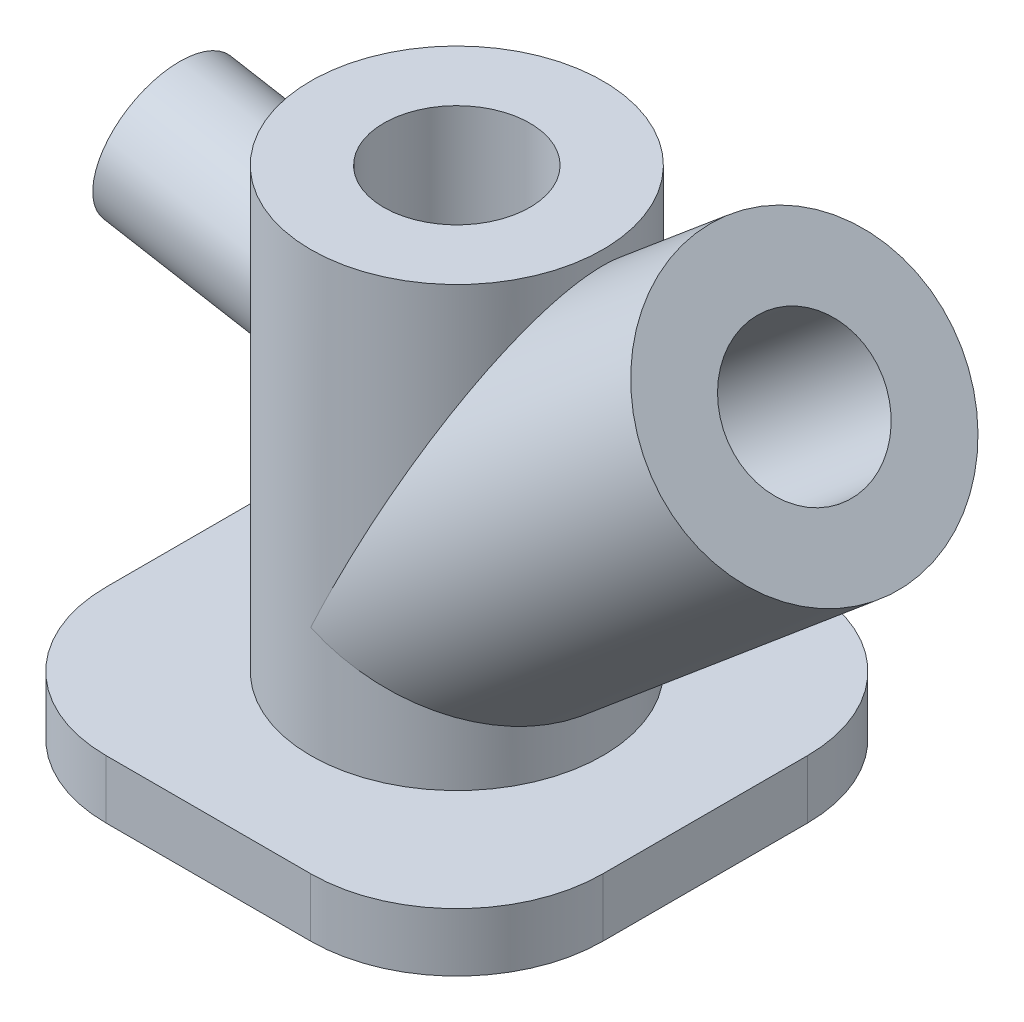
SolidWorks part; units mm, degrees
ref_plane "Front Plane" through (0, 0, 0) normal (0, 0, 1) x (1, 0, 0)
ref_plane "Top Plane" through (0, 0, 0) normal (0, 1, 0) x (1, 0, 0)
ref_plane "Right Plane" through (0, 0, 0) normal (1, 0, 0) x (0, 0, -1)
sketch "Sketch2" plane through (0, 0, 0) normal (0, 1, 0) x (1, 0, 0)
  line L1 (35, -85) -> (-35, -85)
  line L2 (85, -35) -> (85, 35)
  line L3 (35, 85) -> (-35, 85)
  line L4 (-85, -35) -> (-85, 35)
  line L5 (85, -85) -> (-85, 85) construction
  line L6 (85, 85) -> (-85, -85) construction
  arc A0 (-85, 35) -> (-35, 85) centre (-35, 35) cw
  arc A1 (-35, -85) -> (-85, -35) centre (-35, -35) cw
  arc A2 (85, -35) -> (35, -85) centre (35, -35) cw
  arc A3 (35, 85) -> (85, 35) centre (35, 35) cw
  point P0 (0, 0)
  dimension "D3" = 50
  dimension "D4" = 50
  dimension "D5" = 50
  dimension "D6" = 50
  dimension "D1" = 170
  dimension "D2" = 170
extrude "Boss-Extrude1" add sketch "Sketch2" along normal blind 20
sketch "Sketch3" plane through (0, 20, 0) normal (0, 1, 0) x (1, 0, 0)
  circle A0 centre (0, 0) radius 50
extrude "Boss-Extrude2" add sketch "Sketch3" along normal blind 150
sketch "Sketch4" plane through (0, 170, 0) normal (0, 1, 0) x (1, 0, 0)
  circle A0 centre (0, 0) radius 25
extrude "Cut-Extrude1" cut sketch "Sketch4" against normal blind 170
sketch "Sketch5" plane through (0, 0, 0) normal (0, 0, 1) x (1, 0, 0)
  line L0 (50, 100) -> (118.944, 157.8509) construction
  line L1 (98.4197, 182.3108) -> (154.7708, 115.1542) construction
  line L2 (50, 20) -> (50, 170) construction
  line L3 (85, 20) -> (35, 20) construction
  point P6 (0, 0)
  point P7 (0, 0)
  point P10 (0, 0)
  dimension "D1" = 80
  dimension "D2" = 130
  dimension "D3" = 90
ref_plane "Plane1" through (147.5256, 123.7887, 0) normal (0.766, 0.6428, 0) x (0, 0, -1)
sketch "Sketch6" plane through (147.5256, 123.7887, 0) normal (0.766, 0.6428, 0) x (0, 0, -1)
  circle A0 centre (0, 44.4651) radius 50
extrude "Boss-Extrude4" add sketch "Sketch6" against normal up to next
sketch "Sketch7" plane through (147.5256, 123.7887, 0) normal (0.766, 0.6428, 0) x (0, 0, -1)
  circle A0 centre (0, 44.4651) radius 25
extrude "Cut-Extrude2" cut sketch "Sketch7" against normal up to next and the other way through all
sketch "Sketch8" plane through (0, 0, 0) normal (0, 0, 1) x (1, 0, 0)
  line L0 (-99.2404, 128.6824) -> (-50, 120) construction
  line L1 (-102.3273, 111.1759) -> (-95.4373, 150.2509) construction
  line L2 (-50, 170) -> (-50, 20) construction
  dimension "D1" = 100
  dimension "D2" = 50
  dimension "D3" = 100
ref_plane "Plane2" through (-118.2539, 20.8514, 0) normal (0.9848, -0.1736, 0) x (0, 0, -1)
sketch "Sketch9" plane through (-118.2539, 20.8514, 0) normal (0.9848, -0.1736, 0) x (0, 0, -1)
  circle A0 centre (0, 109.4945) radius 25
extrude "Boss-Extrude5" add sketch "Sketch9" along normal up to next
sketch "Sketch10" plane through (-118.2539, 20.8514, 0) normal (-0.9848, 0.1736, 0) x (0, 0, 1)
  circle A0 centre (0, 109.4945) radius 12.5
extrude "Cut-Extrude3" cut sketch "Sketch10" against normal up to next
